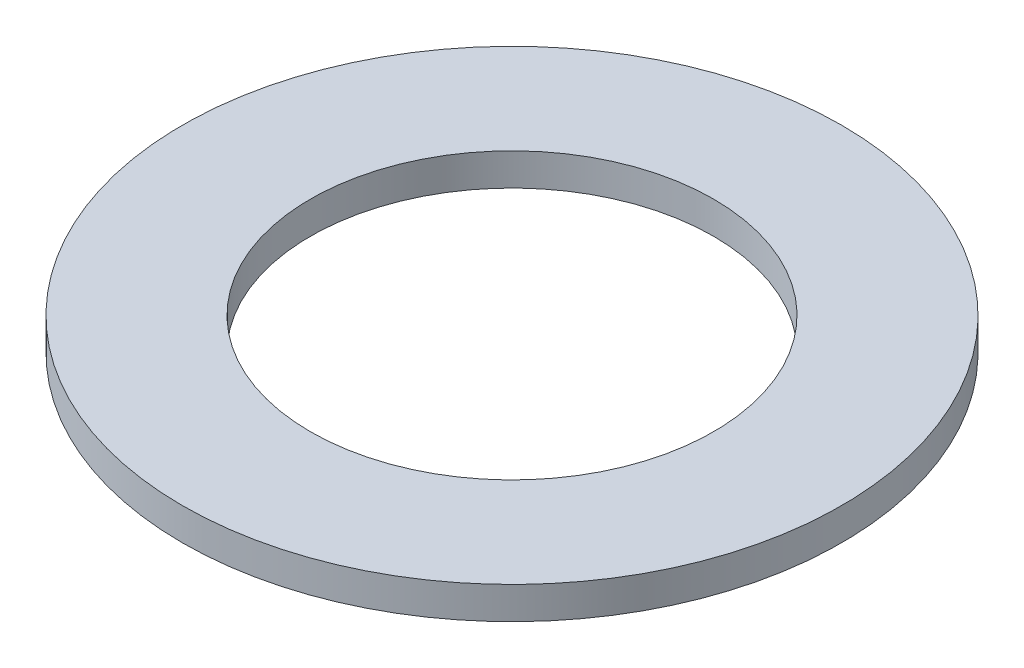
SolidWorks part; units mm, degrees
ref_plane "Front Plane" through (0, 0, 0) normal (0, 0, 1) x (1, 0, 0)
ref_plane "Top Plane" through (0, 0, 0) normal (0, 1, 0) x (1, 0, 0)
ref_plane "Right Plane" through (0, 0, 0) normal (1, 0, 0) x (0, 0, -1)
sketch "Sketch2" plane through (0, 0, 0) normal (0, 1, 0) x (1, 0, 0)
  circle A0 centre (0, 0) radius 5
  circle A1 centre (0, 0) radius 8.175
  point P2 (0, 0)
  point P4 (0, 0)
  dimension "D1" = 3.175
extrude "Boss-Extrude2" add sketch "Sketch2" along normal blind 0.8 contours A1 A0
